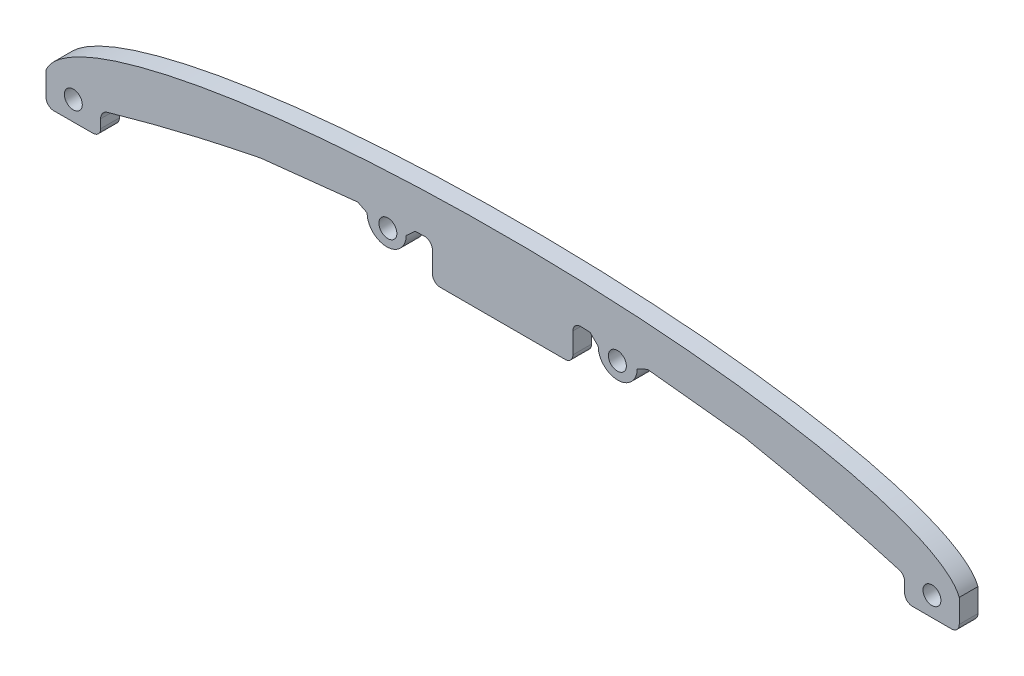
SolidWorks part; units mm, degrees
ref_plane "Płaszczyzna przednia" through (0, 0, 0) normal (0, 0, 1) x (1, 0, 0)
ref_plane "Płaszczyzna górna" through (0, 0, 0) normal (0, 1, 0) x (1, 0, 0)
ref_plane "Płaszczyzna prawa" through (0, 0, 0) normal (1, 0, 0) x (0, 0, -1)
sketch "Szkic1" plane through (0, 0, 0) normal (0, 0, 1) x (1, 0, 0)
  line L6 (-10.0387, 6.8116) -> (-11.2011, 6.7658)
  line L7 (10.0399, 6.8115) -> (11.2021, 6.7658)
  line L9 (-12.3563, 5.7251) -> (-11.2011, 6.7658)
  line L14 (-17.3563, 5.7251) -> (-18.5545, 6.3293)
  line L15 (12.2437, 5.7251) -> (11.2021, 6.7658)
  line L16 (17.2437, 5.7251) -> (18.5543, 6.3293)
  line L17 (-58.5, 1.0017) -> (-58.5, -2.013)
  line L18 (-57.4978, -3.013) -> (-52.4979, -3.0022)
  line L19 (-51.5, -2.0022) -> (-51.5, -0.8936)
  line L20 (51.5, -0.7468) -> (51.5, -1.9983)
  line L21 (52.5, -2.9983) -> (57.5, -2.9983)
  line L22 (58.5, -1.9983) -> (58.5, 1.0017)
  line L25 (-8.9993, 5.8124) -> (-8.9993, 3.1525)
  line L26 (-7.9993, 2.1525) -> (8.0006, 2.1525)
  line L27 (9.0006, 5.8123) -> (9.0006, 3.1525)
  line L28 (-18.5545, 6.3293) -> (-31, 4.9913)
  line L29 (18.5543, 6.3293) -> (31, 4.9913)
  arc A2 (-17.3563, 5.7251) -> (-12.3563, 5.7251) centre (-14.8563, 5.7251) ccw
  arc A3 (12.2437, 5.7251) -> (17.2437, 5.7251) centre (14.7437, 5.7251) ccw
  arc A4 (-51.5, -0.8936) -> (-50.6394, 0.2487) centre (-50.3117, -0.8936) cw
  arc A5 (51.5, -0.7468) -> (50.7802, 0.2132) centre (50.5, -0.7468) ccw
  arc A6 (52.5, -2.9983) -> (51.5, -1.9983) centre (52.5, -1.9983) cw
  arc A7 (57.5, -2.9983) -> (58.5, -1.9983) centre (57.5, -1.9983) ccw
  arc A8 (-57.4978, -3.013) -> (-58.5, -2.013) centre (-57.5, -2.013) cw
  arc A9 (-52.4979, -3.0022) -> (-51.5, -2.0022) centre (-52.5, -2.0022) ccw
  arc A10 (-7.9993, 2.1525) -> (-8.9993, 3.1525) centre (-7.9993, 3.1525) cw
  arc A11 (8.0006, 2.1525) -> (9.0006, 3.1525) centre (8.0006, 3.1525) ccw
  arc A12 (9.0006, 5.8123) -> (10.0399, 6.8115) centre (10.0006, 5.8123) cw
  arc A13 (-8.9993, 5.8124) -> (-10.0387, 6.8116) centre (-9.9993, 5.8124) ccw
  ellipse E0 centre (0, 0) end of major axis (-58.7035, 0) minor radius 12.0417 (58.5, 1.0017) -> (-58.5, 1.0017) ccw
  spline S2 degree 3 poles (-31, 4.9913) (-37.6137, 3.6886) (-44.1607, 2.1076) (-50.6394, 0.2487) knots 0 0 0 0 0.957581 0.957581 0.957581 0.957581
  spline S3 degree 3 poles (31, 4.9913) (37.6689, 3.7084) (44.2623, 2.1157) (50.7802, 0.2132) knots 0 0 0 0 0.96448 0.96448 0.96448 0.96448
  point P39 (51.5, -2.9983)
  point P42 (58.5, -2.9983)
  point P45 (-58.5, -3.0151)
  point P48 (-51.5, -3)
  dimension "D2" = 7
  dimension "D1" = 1.1883
  dimension "D4" = 1
  dimension "D5" = 1
  dimension "D3" = 7
extrude "Boss-Extrude2" add sketch "Szkic1" along normal blind 2.4
sketch "Sketch1" plane through (0, 0, 2.4) normal (0, 0, 1) x (1, 0, 0)
  line L0 (-58.5, 1.0017) -> (-58.5, -2.013) construction
  line L1 (-57.4978, -3.013) -> (-52.4979, -3.0022) construction
  line L2 (58.5, -1.9983) -> (58.5, 1.0017) construction
  line L3 (-7.9993, 2.1525) -> (8.0006, 2.1525) construction
  line L4 (-8.9993, 5.8124) -> (-8.9993, 3.1525) construction
  line L5 (9.0006, 3.1525) -> (9.0006, 5.8123) construction
  circle A0 centre (-55, -0.5076) radius 1.15
  circle A1 centre (-14.6993, 5.3525) radius 1.15
  circle A2 centre (14.7006, 5.3525) radius 1.15
  circle A4 centre (55, -0.5076) radius 1.15
  point P6 (0, 0)
  point P17 (0, 0)
  dimension "D1" = 2.3
  dimension "D4" = 3.5
  dimension "D2" = 3.5
  dimension "D3" = 2.5
  dimension "D5" = 3.2
  dimension "D6" = 5.7
  dimension "D7" = 5.7
extrude "Cut-Extrude1" cut sketch "Sketch1" against normal blind 2.4
